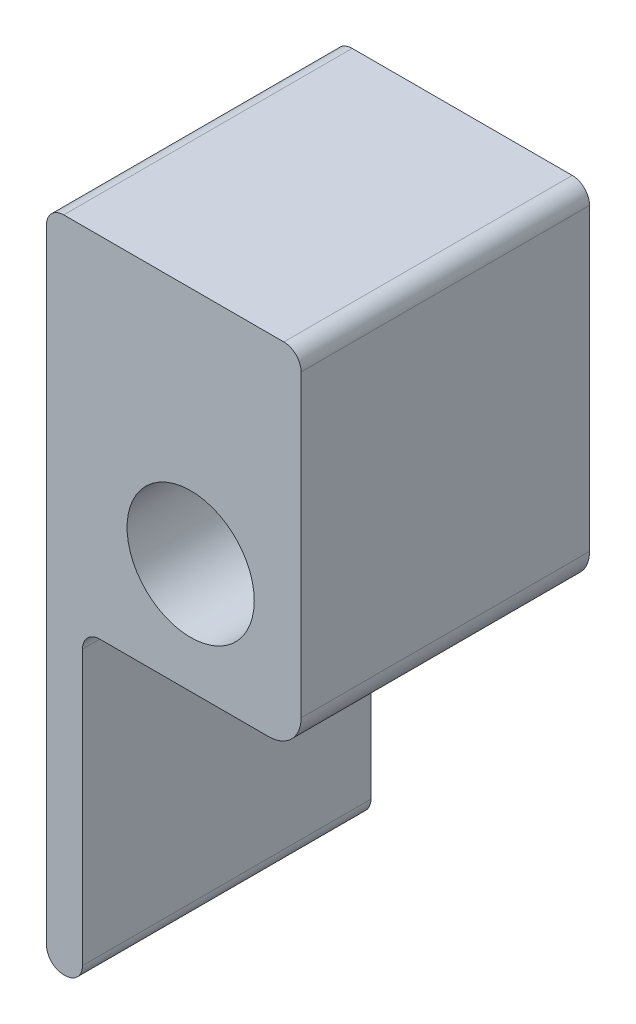
SolidWorks part; units mm, degrees
material "Bambu PAHT-CF"
ref_plane "Front Plane" through (0, 0, 0) normal (0, 0, 1) x (1, 0, 0)
ref_plane "Top Plane" through (0, 0, 0) normal (0, 1, 0) x (1, 0, 0)
ref_plane "Right Plane" through (0, 0, 0) normal (1, 0, 0) x (0, 0, -1)
sketch "Sketch1" plane through (0, 0, 0) normal (0, 0, 1) x (1, 0, 0)
  line L0 (-25.4, -19.455) -> (-25.4, 19.455)
  line L5 (-25.4, -19.455) -> (0, -19.455) construction
  line L6 (-25.4, 19.455) -> (0, 19.455) construction
  line L15 (0, -11.2) -> (0, -19.455) construction
  line L16 (0, 11.2) -> (0, 19.455) construction
  line L17 (11.2, 0) -> (19.455, 0) construction
  line L18 (0, 19.455) -> (19.455, 19.455) construction
  line L19 (19.455, 19.455) -> (19.455, 0)
  line L20 (19.455, 0) -> (19.455, -13.74)
  line L21 (13.74, -19.455) -> (0, -19.455)
  line L24 (-25.4, -19.455) -> (-25.4, -70.782)
  line L25 (-22.352, -73.83) -> (-22.098, -73.83)
  line L26 (-19.05, -22.503) -> (-19.05, -70.782)
  line L27 (-16.002, -19.455) -> (0, -19.455)
  line L29 (-25.4, 19.455) -> (-25.4, 39.032)
  line L30 (-22.352, 42.08) -> (16.407, 42.08)
  line L31 (19.455, 19.455) -> (19.455, 39.032)
  circle A0 centre (0, 0) radius 11.2
  arc A8 (19.455, -13.74) -> (13.74, -19.455) centre (13.74, -13.74) cw
  arc A12 (16.407, 42.08) -> (19.455, 39.032) centre (16.407, 39.032) cw
  arc A13 (-25.4, 39.032) -> (-22.352, 42.08) centre (-22.352, 39.032) cw
  arc A14 (-25.4, -70.782) -> (-22.352, -73.83) centre (-22.352, -70.782) ccw
  arc A15 (-22.098, -73.83) -> (-19.05, -70.782) centre (-22.098, -70.782) ccw
  arc A16 (-16.002, -19.455) -> (-19.05, -22.503) centre (-16.002, -22.503) ccw
  point P6 (-19.05, -19.455)
  point P12 (0, 11.2)
  point P18 (-25.4, 42.08)
  point P20 (0, -11.2)
  point P22 (11.2, 0)
  point P23 (-25.4, -73.83)
  point P31 (-19.05, -73.83)
  point P34 (-19.05, -19.455)
  dimension "D1" = 22.4
  dimension "D5" = 5.715
  dimension "D6" = 6.35
  dimension "D8" = 3.048
  dimension "D2" = 25.4
  dimension "D3" = 8.255
  dimension "D4" = 54.375
  dimension "D7" = 22.625
extrude "Boss-Extrude1" add sketch "Sketch1" along normal blind 50.8
